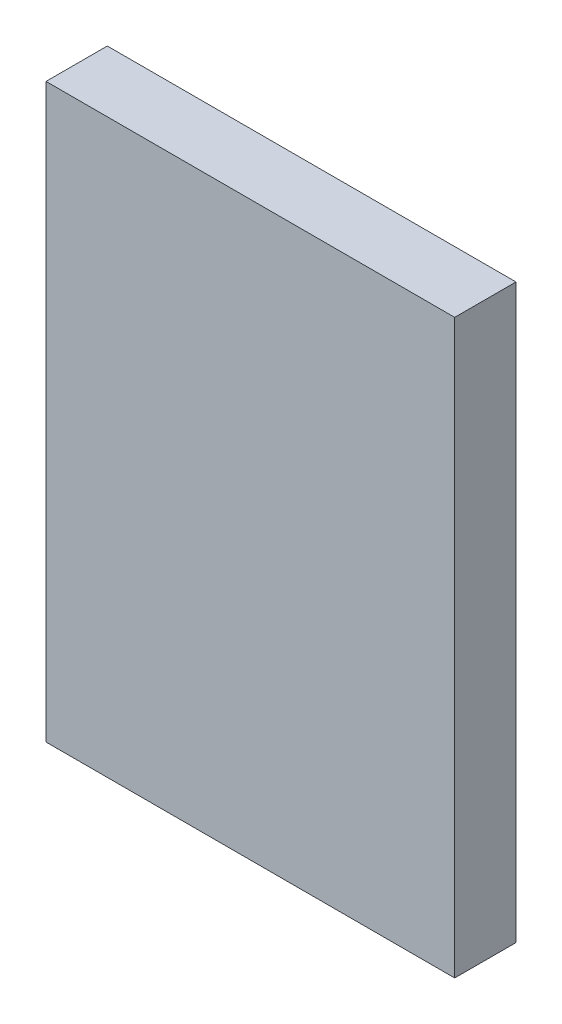
SolidWorks part; units mm, degrees
material "Клен"
ref_plane "Спереди" through (0, 0, 0) normal (0, 0, 1) x (1, 0, 0)
ref_plane "Сверху" through (0, 0, 0) normal (0, 1, 0) x (1, 0, 0)
ref_plane "Справа" through (0, 0, 0) normal (1, 0, 0) x (0, 0, -1)
sketch "Эскиз2" plane through (0, 0, 0) normal (0, 0, 1) x (1, 0, 0)
  line L5 (20, 8) -> (-20, 8)
  line L6 (20, 8) -> (20, -48)
  line L7 (20, -48) -> (-20, -48)
  line L8 (-20, 8) -> (-20, -48)
extrude "Бобышка-Вытянуть1" add sketch "Эскиз2" along normal blind 6
